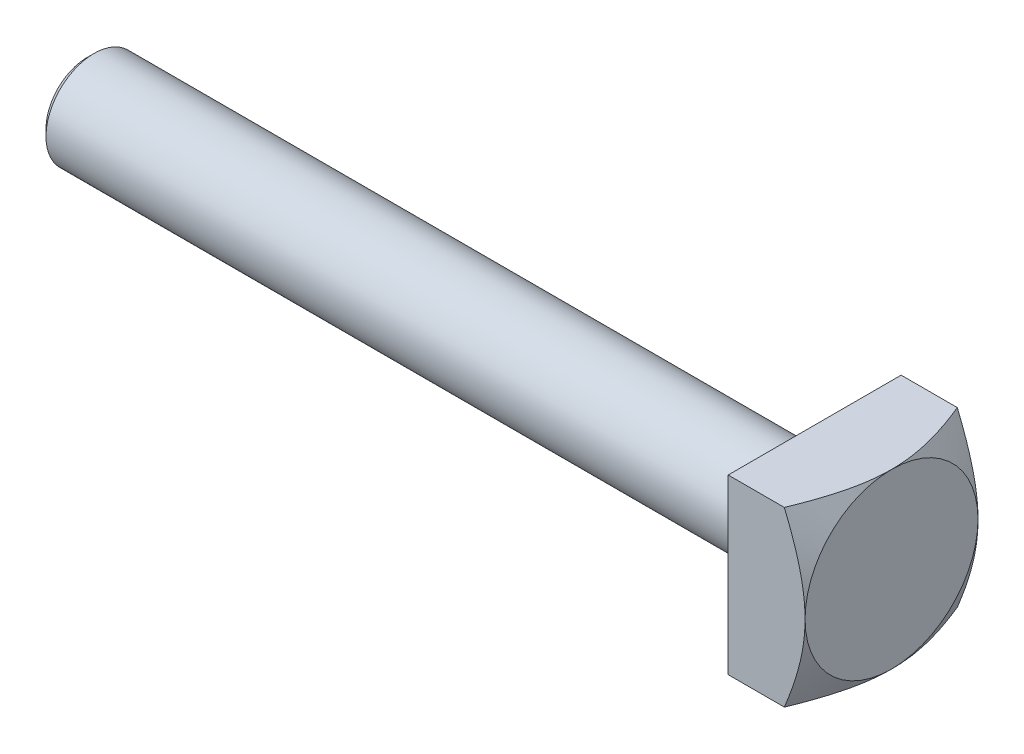
SolidWorks part; units mm, degrees
ref_plane "Front Plane" through (0, 0, 0) normal (0, 0, 1) x (1, 0, 0)
ref_plane "Top Plane" through (0, 0, 0) normal (0, 1, 0) x (1, 0, 0)
ref_plane "Right Plane" through (0, 0, 0) normal (1, 0, 0) x (0, 0, -1)
sketch "Sketch1" plane through (0, 0, 0) normal (0, 0, 1) x (1, 0, 0)
  line L0 (-59.9734, 0) -> (41.3325, 0) construction
  line L1 (-33.6675, 5) -> (-34.3746, 4.2929)
  line L2 (-34.3746, 4.2929) -> (-34.3746, 0)
  line L3 (-33.6675, 5) -> (41.3325, 5)
  line L7 (-34.3746, 0) -> (41.3325, 0)
  line L8 (41.3325, 5) -> (41.3325, 0)
  dimension "D1" = 135
  dimension "D2" = 5
  dimension "D3" = 1
  dimension "D4" = 75
revolve "Revolve1" add sketch "Sketch1" angle 360 about L0
cosmetic thread "Cosmetic Thread1" parameters "D1"=26, "D2"=9
sketch "Sketch3" plane through (0, 0, 0) normal (0, 0, 1) x (1, 0, 0)
  line L0 (-8.3746, 5) -> (-8.3746, -5)
  line L1 (41.3325, 5) -> (-33.6675, 5) construction
  line L2 (-33.6675, -5) -> (41.3325, -5) construction
  line L3 (-34.3746, 4.2929) -> (-34.3746, -4.2929) construction
  dimension "D1" = 26
sketch "Sketch4" plane through (41.3325, 0, 0) normal (1, 0, 0) x (0, 0, -1)
  line L1 (-9, 9) -> (9, 9)
  line L2 (-9, 9) -> (-9, -9)
  line L3 (-9, -9) -> (9, -9)
  line L4 (9, 9) -> (9, -9)
  line L5 (-9, 9) -> (9, -9) construction
  line L6 (-9, -9) -> (9, 9) construction
  point P0 (0, 0)
  dimension "D1" = 18
  dimension "D2" = 18
extrude "Boss-Extrude1" add sketch "Sketch4" along normal blind 8
sketch "Sketch5" plane through (49.3325, 0, 0) normal (1, 0, 0) x (0, 0, -1)
  circle A0 centre (0, 0) radius 9
extrude "Cut-Extrude3" cut sketch "Sketch5" against normal blind 10 draft 60 flip side to cut
